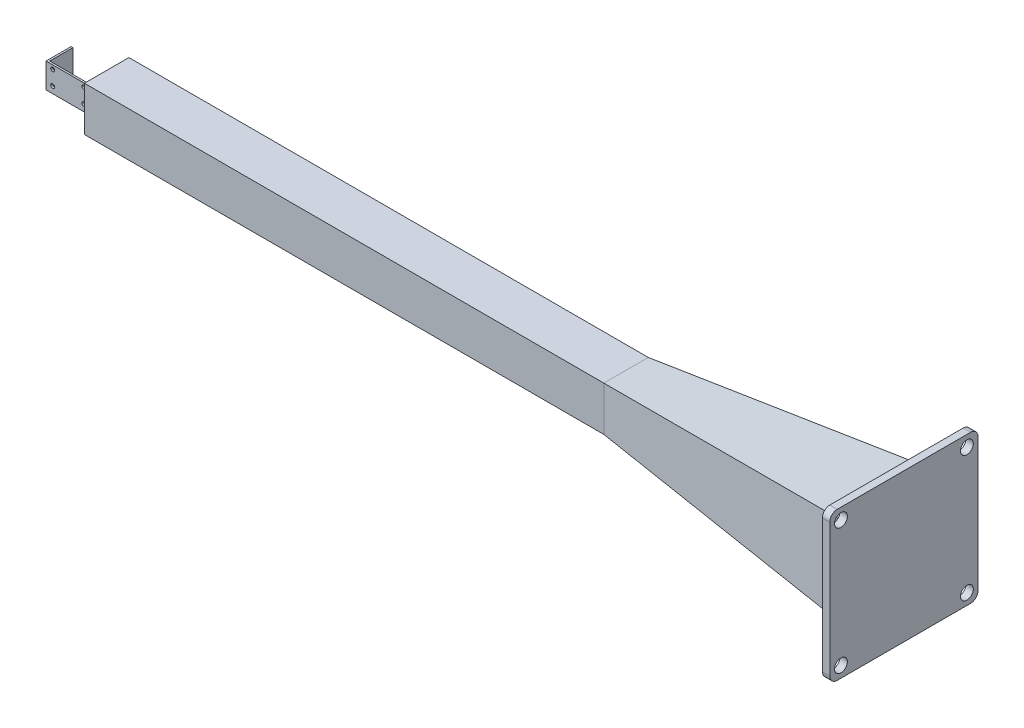
SolidWorks part; units mm, degrees
material "1023 Carbon Steel Sheet (SS)"
ref_plane "Front Plane" through (0, 0, 0) normal (0, 0, 1) x (1, 0, 0)
ref_plane "Top Plane" through (0, 0, 0) normal (0, 1, 0) x (1, 0, 0)
ref_plane "Right Plane" through (0, 0, 0) normal (1, 0, 0) x (0, 0, -1)
sketch "Sketch1" plane through (0, 0, 0) normal (0, 0, 1) x (1, 0, 0)
  line L264 (-103.7607, 63.7322) -> (-103.7607, -66.2678)
  line L265 (116.2393, 63.7322) -> (116.2393, -66.2678)
  line L267 (116.2393, 63.7322) -> (-103.7607, 63.7322)
  line L269 (116.2393, -66.2678) -> (-103.7607, -66.2678)
  circle A2 centre (90.2393, -40.2678) radius 10.5
  circle A3 centre (-77.7607, -40.2678) radius 10.5
  circle A4 centre (-77.7607, 37.7322) radius 10.5
  circle A5 centre (90.2393, 37.7322) radius 10.5
extrude "Boss-Extrude1" add sketch "Sketch1" along normal blind 10
sketch "Sketch2" plane through (0, 0, 10) normal (0, 0, 1) x (1, 0, 0)
  line L3 (-103.7607, 63.7322) -> (-113.7607, 63.7322)
  line L4 (-103.7607, 63.7322) -> (-103.7607, -66.2678)
  line L6 (-113.7607, 63.7322) -> (-113.7607, -66.2678)
  line L7 (-103.7607, -66.2678) -> (116.2393, -66.2678)
  line L8 (-113.7607, -66.2678) -> (-113.7607, -76.2678)
  line L9 (-113.7607, -76.2678) -> (116.2393, -76.2678)
  line L10 (116.2393, -66.2678) -> (116.2393, -76.2678)
extrude "Boss-Extrude2" add sketch "Sketch2" against normal blind 250
sketch "Sketch3" plane through (0, 63.7322, 0) normal (0, 1, 0) x (1, 0, 0)
  line L6 (116.2393, 0) -> (-103.7607, 0)
  line L7 (-103.7607, 0) -> (-103.7607, 240)
  line L8 (-103.7607, 240) -> (-113.7607, 240)
  line L9 (-113.7607, 240) -> (-113.7607, -10)
  line L10 (-113.7607, -10) -> (116.2393, -10)
  line L11 (116.2393, -10) -> (116.2393, 0)
  line L12 (116.2393, 0) -> (-103.7607, 0)
  line L13 (-103.7607, 0) -> (-103.7607, 240)
  line L14 (-103.7607, 240) -> (-113.7607, 240)
  line L15 (-113.7607, 240) -> (-113.7607, -10)
  line L16 (-113.7607, -10) -> (116.2393, -10)
  line L17 (116.2393, -10) -> (116.2393, 0)
  dimension "D1" = 0
extrude "Cut-Extrude1" cut sketch "Sketch3" against normal blind 5
sketch "Sketch4" plane through (0, 0, 10) normal (0, 0, 1) x (1, 0, 0)
  line L0 (-113.7607, -76.2678) -> (116.2393, -76.2678) construction
  line L1 (-113.7607, -76.2678) -> (116.2393, -76.2678)
  line L3 (116.2393, 58.7322) -> (126.2393, 58.7322)
  line L4 (116.2393, 58.7322) -> (116.2393, -76.2678)
  line L5 (116.2393, -76.2678) -> (126.2393, -76.2678)
  line L6 (126.2393, 58.7322) -> (126.2393, -76.2678)
  line M5 (116.2393, -76.2678) -> (116.2393, 58.7322)
extrude "Boss-Extrude3" add sketch "Sketch4" against normal up to surface (250 mm away) contours L6 L3 L5 M5 up to face at (-33.7607, -27.9344, -240)
sketch "Sketch5" plane through (126.2393, 0, 0) normal (1, 0, 0) x (0, 0, -1)
  line L4 (240, -76.2678) -> (240, 58.7322)
  line L5 (240, 58.7322) -> (-10, 58.7322)
  line L6 (-10, 58.7322) -> (-10, -76.2678)
  line L7 (-10, -76.2678) -> (240, -76.2678)
  line L8 (240, -76.2678) -> (240, 58.7322)
  line L9 (240, 58.7322) -> (-10, 58.7322)
  line L10 (-10, 58.7322) -> (-10, -76.2678)
  line L11 (-10, -76.2678) -> (240, -76.2678)
  dimension "D1" = 0
extrude "Boss-Extrude4" add sketch "Sketch5" along normal blind 2800 separate body
sketch "Sketch8" plane through (2926.2393, 0, 0) normal (1, 0, 0) x (0, 0, -1)
  line L0 (-10, -76.2678) -> (240, -76.2678) construction
  line L1 (-10, 58.7322) -> (125, 58.7322)
  line L2 (-10, 58.7322) -> (-10, -76.2678)
  line L3 (-10, -76.2678) -> (125, -76.2678)
  line L4 (125, 58.7322) -> (125, -76.2678)
  line L6 (125, 58.7322) -> (240, 58.7322)
  line L7 (125, 58.7322) -> (125, -76.2678)
  line L8 (125, -76.2678) -> (240, -76.2678)
  line L9 (240, 58.7322) -> (240, -76.2678)
  line M9 (-10, -76.2678) -> (240, -76.2678)
  line M10 (240, -76.2678) -> (240, 58.7322)
  line M11 (240, 58.7322) -> (-10, 58.7322)
extrude "Cut-Extrude2" cut sketch "Sketch8" against normal blind 10000 contours L4 M11 M9 M10
sketch "Sketch12" plane through (2926.2393, 0, 0) normal (1, 0, 0) x (0, 0, -1)
  line L2 (-27.5, 76.2322) -> (142.5, 76.2322)
  line L3 (-27.5, 76.2322) -> (-27.5, -93.7678)
  line L4 (-27.5, -93.7678) -> (142.5, -93.7678)
  line L5 (142.5, 76.2322) -> (142.5, -93.7678)
  line L6 (-27.5, 76.2322) -> (142.5, -93.7678) construction
  line L7 (-27.5, -93.7678) -> (142.5, 76.2322) construction
  point P4 (57.5, -8.7678)
extrude "Boss-Extrude6" add sketch "Sketch12" against normal up to vertex (2800 mm away)
sketch "Sketch14" plane through (0, -76.2678, 0) normal (0, -1, 0) x (1, 0, 0)
  line L0 (-103.7607, 0) -> (116.2393, 0)
  line L5 (116.2393, 0) -> (116.2393, -115)
  line L7 (-103.7607, 0) -> (-103.7607, -115)
  line L8 (116.2393, -115) -> (116.2393, -125)
  line L12 (116.2393, -125) -> (-103.7607, -125)
  line L13 (-103.7607, -125) -> (-103.7607, -115)
extrude "Cut-Extrude3" cut sketch "Sketch14" against normal blind 50
sketch "Sketch15" plane through (2926.2393, 0, 0) normal (1, 0, 0) x (0, 0, -1)
  line L4 (142.5, -93.7678) -> (142.5, 76.2322)
  line L5 (142.5, 76.2322) -> (-27.5, 76.2322)
  line L6 (-27.5, 76.2322) -> (-27.5, -93.7678)
  line L7 (-27.5, -93.7678) -> (142.5, -93.7678)
  line L8 (142.5, -93.7678) -> (142.5, 76.2322)
  line L9 (142.5, 76.2322) -> (-27.5, 76.2322)
  line L10 (-27.5, 76.2322) -> (-27.5, -93.7678)
  line L11 (-27.5, -93.7678) -> (142.5, -93.7678)
  dimension "D1" = 0
extrude "Boss-Extrude7" add sketch "Sketch15" along normal blind 1524
sketch "Sketch16" plane through (126.2393, 0, 0) normal (-1, 0, 0) x (0, 0, 1)
  line L2 (-177.5, 111.2322) -> (62.5, 111.2322)
  line L3 (-177.5, 111.2322) -> (-177.5, -128.7678)
  line L4 (-177.5, -128.7678) -> (62.5, -128.7678)
  line L5 (62.5, 111.2322) -> (62.5, -128.7678)
  line L6 (-177.5, 111.2322) -> (62.5, -128.7678) construction
  line L7 (-177.5, -128.7678) -> (62.5, 111.2322) construction
  point P4 (-57.5, -8.7678)
extrude "Boss-Extrude8" add sketch "Sketch16" against normal up to surface (4324 mm away) up to face at (4450.2393, -8.7678, -57.5)
sketch "Sketch17" plane through (126.2393, 0, 0) normal (-1, 0, 0) x (0, 0, 1)
  line L4 (62.5, -128.7678) -> (62.5, 111.2322)
  line L5 (62.5, 111.2322) -> (-177.5, 111.2322)
  line L6 (-177.5, 111.2322) -> (-177.5, -128.7678)
  line L7 (-177.5, -128.7678) -> (62.5, -128.7678)
  line L8 (62.5, -128.7678) -> (62.5, 111.2322)
  line L9 (62.5, 111.2322) -> (-177.5, 111.2322)
  line L10 (-177.5, 111.2322) -> (-177.5, -128.7678)
  line L11 (-177.5, -128.7678) -> (62.5, -128.7678)
  dimension "D1" = 0
extrude "Cut-Extrude4" cut sketch "Sketch17" against normal blind 20
sketch "Sketch18" plane through (126.2393, 0, 0) normal (1, 0, 0) x (0, 0, -1)
  line L4 (-10, -76.2678) -> (125, -76.2678)
  line L5 (125, -76.2678) -> (125, 58.7322)
  line L6 (125, 58.7322) -> (-10, 58.7322)
  line L7 (-10, 58.7322) -> (-10, -76.2678)
  line L8 (-10, -76.2678) -> (125, -76.2678)
  line L9 (125, -76.2678) -> (125, 58.7322)
  line L10 (125, 58.7322) -> (-10, 58.7322)
  line L11 (-10, 58.7322) -> (-10, -76.2678)
  dimension "D1" = 0
extrude "Boss-Extrude9" add sketch "Sketch18" along normal up to surface (20 mm away) up to face at (146.2393, -8.7678, -57.5)
sketch "Sketch19" plane through (4450.2393, 0, 0) normal (1, 0, 0) x (0, 0, -1)
  line L2 (-192.5, 241.2322) -> (307.5, 241.2322)
  line L3 (-192.5, 241.2322) -> (-192.5, -258.7678)
  line L4 (-192.5, -258.7678) -> (307.5, -258.7678)
  line L5 (307.5, 241.2322) -> (307.5, -258.7678)
  point P0 (0, 0)
ref_plane "Plane1" through (2950.2393, 0, 0) normal (1, 0, 0) x (0, 0, -1)
sketch "Sketch20" plane through (2950.2393, 0, 0) normal (1, 0, 0) x (0, 0, -1)
  line L4 (-62.5, 111.2322) -> (-62.5, -128.7678)
  line L5 (-62.5, -128.7678) -> (177.5, -128.7678)
  line L6 (177.5, -128.7678) -> (177.5, 111.2322)
  line L7 (177.5, 111.2322) -> (-62.5, 111.2322)
  line L8 (-62.5, 111.2322) -> (-62.5, -128.7678)
  line L9 (-62.5, -128.7678) -> (177.5, -128.7678)
  line L10 (177.5, -128.7678) -> (177.5, 111.2322)
  line L11 (177.5, 111.2322) -> (-62.5, 111.2322)
  dimension "D1" = 0
loft "Loft1" add profiles "Sketch19", "Sketch20"
sketch "Sketch21" plane through (4450.2393, 0, 0) normal (1, 0, 0) x (0, 0, -1)
  line L2 (417.5, -408.7678) -> (-302.5, -408.7678)
  line L3 (457.5, -368.7678) -> (457.5, 351.2322)
  line L4 (417.5, 391.2322) -> (-302.5, 391.2322)
  line L5 (-342.5, -368.7678) -> (-342.5, 351.2322)
  circle A0 centre (397.3959, -348.6637) radius 34.7575
  circle A1 centre (-282.3959, -348.6637) radius 34.7575
  circle A2 centre (-282.3959, 331.1281) radius 34.7575
  circle A3 centre (397.3959, 331.1281) radius 34.7575
  arc A4 (-342.5, 351.2322) -> (-302.5, 391.2322) centre (-302.5, 351.2322) cw
  arc A5 (-302.5, -408.7678) -> (-342.5, -368.7678) centre (-302.5, -368.7678) cw
  arc A6 (457.5, -368.7678) -> (417.5, -408.7678) centre (417.5, -368.7678) cw
  arc A7 (457.5, 351.2322) -> (417.5, 391.2322) centre (417.5, 351.2322) ccw
  point P4 (57.5, -8.7678)
  dimension "D1" = 40
extrude "Boss-Extrude10" add sketch "Sketch21" against normal blind 40
